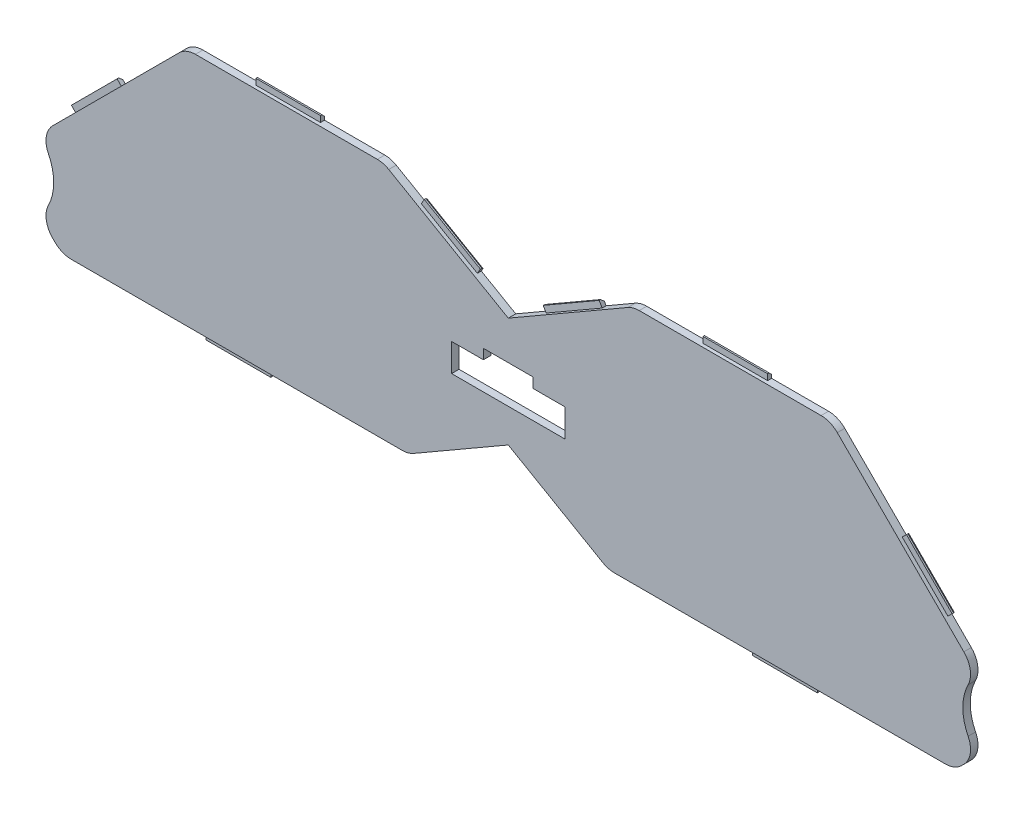
SolidWorks part; units mm, degrees
ref_plane "Front Plane" through (0, 0, 0) normal (0, 0, 1) x (1, 0, 0)
ref_plane "Top Plane" through (0, 0, 0) normal (0, 1, 0) x (1, 0, 0)
ref_plane "Right Plane" through (0, 0, 0) normal (1, 0, 0) x (0, 0, -1)
sketch "Sketch1" plane through (0, 0, 0) normal (0, 0, 1) x (1, 0, 0)
  line L0 (0, 0) -> (0, 23.0192) construction
  line L5 (0, 23.0192) -> (25, 37.453) construction
  line L6 (25, 37.453) -> (65, 37.453) construction
  line L7 (65, 37.453) -> (102, 0.453) construction
  line L8 (102, 0.453) -> (90, -11.547) construction
  line L9 (90, -11.547) -> (20, -11.547) construction
  line L10 (20, -11.547) -> (0, 0) construction
  line L11 (0, 22.5574) -> (25.1072, 37.053)
  line L12 (25.1072, 37.053) -> (64.8343, 37.053)
  line L13 (64.8343, 37.053) -> (101.4343, 0.453)
  line L14 (101.4343, 0.453) -> (89.8343, -11.147)
  line L15 (89.8343, -11.147) -> (20.1072, -11.147)
  line L16 (20.1072, -11.147) -> (0, 0.4619)
  line L17 (0.2, 22.6728) -> (25.1072, 37.053) construction
  line L18 (20.1072, -11.147) -> (0.2, 0.3464) construction
  line L19 (0, 0.4619) -> (0, 22.5574)
  dimension "D1" = 70
  dimension "D2" = 40
  dimension "D3" = 25
  dimension "D4" = 20
  dimension "D5" = 12
  dimension "D6" = 45
  dimension "D7" = 90
  dimension "D8" = 120
  dimension "D9" = 120
  dimension "D10" = 0.4
extrude "Boss-Extrude1" add sketch "Sketch1" along normal blind 1.5
sketch "Sketch5" plane through (0, 0, 0) normal (0, 0, -1) x (-1, 0, 0)
  line L5 (-64.8343, 37.053) -> (-25.1072, 37.053) construction
  line L7 (-51.4707, 37.053) -> (-38.4707, 37.053)
  line L8 (-51.4707, 37.053) -> (-51.4707, 38.253)
  line L9 (-51.4707, 38.253) -> (-38.4707, 38.253)
  line L10 (-38.4707, 37.053) -> (-38.4707, 38.253)
  line L11 (-20.1072, -11.147) -> (-89.8343, -11.147) construction
  line L12 (-61.4707, -11.147) -> (-48.4707, -11.147)
  line L13 (-61.4707, -11.147) -> (-61.4707, -12.347)
  line L14 (-61.4707, -12.347) -> (-48.4707, -12.347)
  line L15 (-48.4707, -11.147) -> (-48.4707, -12.347)
  line L16 (-78.5381, 23.3492) -> (-87.7305, 14.1568)
  line L17 (-78.5381, 23.3492) -> (-79.3866, 24.1977)
  line L18 (-87.7305, 14.1568) -> (-88.579, 15.0053)
  line L19 (-79.3866, 24.1977) -> (-88.579, 15.0053)
  line L20 (-101.4343, 0.453) -> (-64.8343, 37.053) construction
  line L21 (-18.1828, 33.0552) -> (-6.9244, 26.5552)
  line L22 (-18.1828, 33.0552) -> (-17.5828, 34.0944)
  line L23 (-6.9244, 26.5552) -> (-6.3244, 27.5944)
  line L24 (-17.5828, 34.0944) -> (-6.3244, 27.5944)
  line L25 (-25.1072, 37.053) -> (0, 22.5574) construction
  point P6 (-44.9707, 37.053)
  point P7 (-44.9707, 37.053)
  point P26 (-83.1343, 18.753)
  point P27 (-83.1343, 18.753)
  point P28 (-12.5536, 29.8052)
  point P29 (-12.5536, 29.8052)
  point P30 (-54.9707, -11.147)
  point P31 (-54.9707, -11.147)
  dimension "D1" = 1.2
  dimension "D2" = 13
extrude "Boss-Extrude2" add sketch "Sketch5" against normal blind 0.8
chamfer "Chamfer1" distance 0.5 angle 45 4 edges at (11.9536, 30.8444, 0) (54.9707, -12.347, 0) (83.9828, 19.6015, 0) (44.9707, 38.253, 0)
sketch "Sketch6" plane through (0, 0, 1.5) normal (0, 0, 1) x (1, 0, 0)
  circle A1 centre (101.4343, 0.453) radius 10
  dimension "D1" = 20
extrude "Cut-Extrude3" cut sketch "Sketch6" against normal up to next (1.5 mm away)
mirror "Mirror1" about plane through (0, 0.4619, 1.5) normal (1, 0, 0) of "Cut-Extrude3", "Boss-Extrude2", "Boss-Extrude1", "Chamfer1"
sketch "Sketch2" plane through (0, 0, 1.5) normal (0, 0, 1) x (1, 0, 0)
  line L0 (0, 0) -> (0, 10) construction
  line L1 (11.4, 7.2) -> (-11.4, 7.2)
  line L2 (11.4, 7.2) -> (11.4, 12.8)
  line L3 (11.4, 12.8) -> (5, 12.8)
  line L4 (-11.4, 7.2) -> (-11.4, 12.8)
  line L5 (11.4, 7.2) -> (-11.4, 12.8) construction
  line L6 (11.4, 12.8) -> (-11.4, 7.2) construction
  line L7 (-5, 12.8) -> (-11.4, 12.8)
  line L8 (-5, 14.8) -> (5, 14.8)
  line L9 (-5, 14.8) -> (-5, 12.8)
  line L11 (5, 14.8) -> (5, 12.8)
  line L12 (0, 10) -> (0, 14.8) construction
  point P0 (0, 10)
  dimension "D1" = 22.8
  dimension "D2" = 5.6
  dimension "D3" = 10
  dimension "D4" = 10
  dimension "D5" = 2
extrude "Cut-Extrude1" cut sketch "Sketch2" against normal up to next
fillet "Fillet1" radius 4.6 12 edges at (-89.8343, -11.147, 0.75) (-20.1072, -11.147, 0.75) (-64.8343, 37.053, 0.75) (-25.1072, 37.053, 0.75) (25.1072, 37.053, 0.75) (20.1072, -11.147, 0.75) (89.8343, -11.147, 0.75) (64.8343, 37.053, 0.75) (-94.3632, -6.6181, 0.75) (-94.3632, 7.5241, 0.75) (94.3632, 7.5241, 0.75) (94.3632, -6.6181, 0.75)
